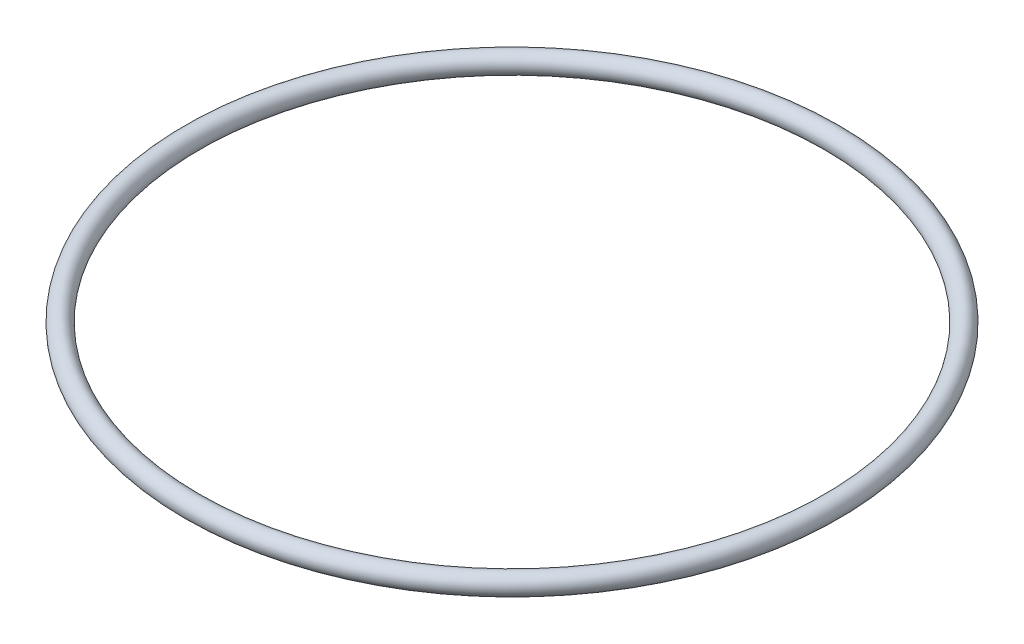
SolidWorks part; units mm, degrees
ref_plane "Front Plane" through (0, 0, 0) normal (0, 0, 1) x (1, 0, 0)
ref_plane "Top Plane" through (0, 0, 0) normal (0, 1, 0) x (1, 0, 0)
ref_plane "Right Plane" through (0, 0, 0) normal (1, 0, 0) x (0, 0, -1)
sketch "Sketch2" plane through (0, 0, 0) normal (0, 1, 0) x (1, 0, 0)
  line L0 (0, 0) -> (0, -74.8441) construction
  line L1 (0, 0) -> (84.2243, 0) construction
  circle A0 centre (0, 0) radius 50.8
  dimension "D1" = 101.6
sweep "Sweep2" add path "Sketch2" circular profile diameter 3.175 parameters "D3"=3.175
